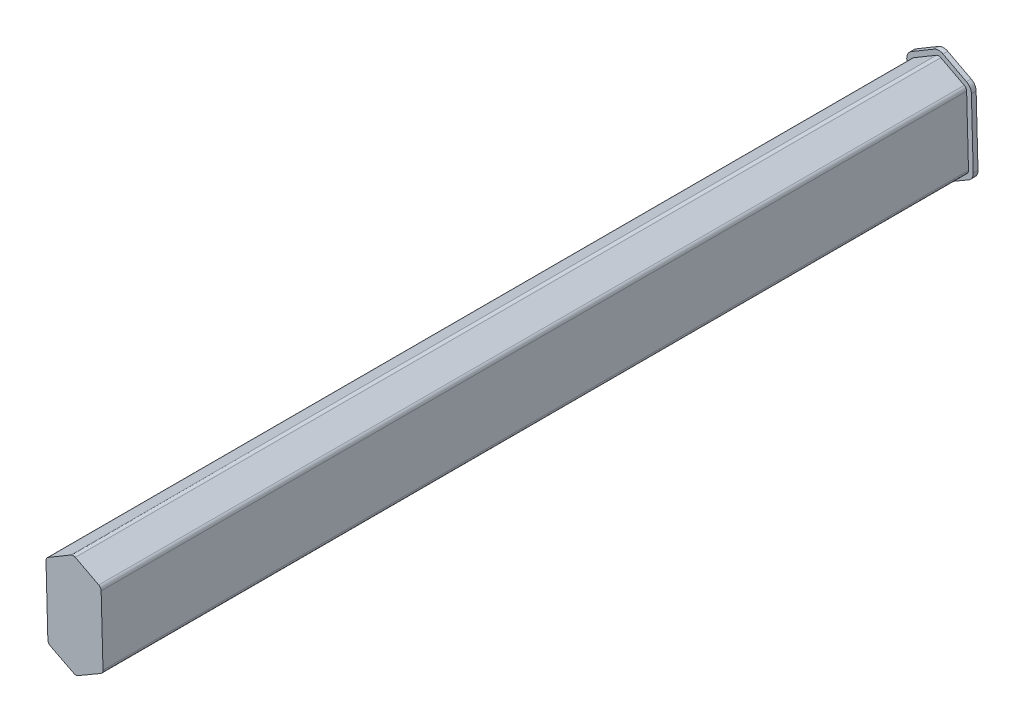
SolidWorks part; units mm, degrees
other "Markup1"
sketch "Sketch4" plane through (238.7089, 157.952, 185) normal (0.151, -0.0403, 0.9877) x (-0.3193, -0.9476, 0.0101)
ref_plane "Front Plane" through (0, 0, 0) normal (0, 0, 1) x (1, 0, 0)
ref_plane "Top Plane" through (0, 0, 0) normal (0, 1, 0) x (1, 0, 0)
ref_plane "Right Plane" through (0, 0, 0) normal (1, 0, 0) x (0, 0, -1)
sketch "Sketch1" plane through (0, 0, 0) normal (0, 0, 1) x (1, 0, 0)
  line L0 (36.798, 101.1427) -> (103.7813, 99.6461) construction
  line L1 (229.8883, 157.752) -> (228.9956, 190.3868) construction
  line L31 (229.4664, 190.0848) -> (234.3884, 187.5166)
  line L32 (228.5166, 190.1025) -> (223.7423, 187.2691) construction
  line L33 (223.253, 186.3818) -> (223.6425, 172.1409) construction
  line L34 (224.1866, 171.2781) -> (229.1073, 168.7597) construction
  line L35 (234.8421, 171.5695) -> (230.0664, 168.7859) construction
  line L36 (234.9486, 186.7017) -> (235.3382, 172.4608) construction
  line L37 (229.4895, 190.1291) -> (234.4116, 187.5609) construction
  line L38 (234.8986, 186.7003) -> (235.2882, 172.4595)
  line L39 (234.8169, 171.6127) -> (230.0413, 168.8291)
  line L40 (224.2093, 171.3226) -> (229.1301, 168.8042)
  line L41 (223.303, 186.3831) -> (223.6925, 172.1423)
  line L42 (228.5421, 190.0595) -> (223.7678, 187.2261)
  arc A0 (223.253, 186.3818) -> (223.7423, 187.2691) centre (224.2526, 186.4091) cw construction
  arc A15 (234.4116, 187.5609) -> (234.9486, 186.7017) centre (233.949, 186.6744) cw construction
  arc A16 (235.3382, 172.4608) -> (234.8421, 171.5695) centre (234.3385, 172.4335) cw construction
  arc A17 (224.1866, 171.2781) -> (223.6425, 172.1409) centre (224.6422, 172.1682) cw construction
  arc A18 (229.1073, 168.7597) -> (230.0664, 168.7859) centre (229.5629, 169.6499) ccw construction
  arc A19 (228.5166, 190.1025) -> (229.4895, 190.1291) centre (229.0269, 189.2425) cw construction
  arc A20 (234.3884, 187.5166) -> (234.8986, 186.7003) centre (233.949, 186.6744) cw
  arc A21 (235.2882, 172.4595) -> (234.8169, 171.6127) centre (234.3385, 172.4335) cw
  arc A22 (229.1301, 168.8042) -> (230.0413, 168.8291) centre (229.5629, 169.6499) ccw
  arc A23 (224.2093, 171.3226) -> (223.6925, 172.1423) centre (224.6422, 172.1682) cw
  arc A24 (223.303, 186.3831) -> (223.7678, 187.2261) centre (224.2526, 186.4091) cw
  arc A25 (228.5421, 190.0595) -> (229.4664, 190.0848) centre (229.0269, 189.2425) cw
  point P24 (223.2369, 186.9692)
  point P27 (234.9326, 187.2891)
  point P30 (235.3544, 171.8681)
  point P33 (223.6588, 171.5482)
  point P36 (229.594, 168.5105)
  point P39 (228.9956, 190.3868)
  dimension "D2" = 0.05
  dimension "D1" = 67
extrude "Boss-Extrude1" add sketch "Sketch1" along normal blind 182 contours L32 A0 L33 A17 L34 A18 L35 A16 L36 A15 L37 A19
sketch "Sketch5" plane through (0, 0, 0) normal (0, 0, -1) x (-1, 0, 0)
  line L25 (-229.929, 190.9713) -> (-234.851, 188.4032)
  line L26 (-235.8983, 186.7277) -> (-236.2878, 172.4868)
  line L27 (-235.3205, 170.7488) -> (-230.5448, 167.9652)
  line L28 (-228.6745, 167.914) -> (-223.7538, 170.4324)
  line L29 (-222.6929, 172.1149) -> (-222.3033, 186.3558)
  line L30 (-223.2574, 188.086) -> (-228.0317, 190.9195)
  line L31 (-229.929, 190.9713) -> (-234.851, 188.4032)
  line L32 (-235.8983, 186.7277) -> (-236.2878, 172.4868)
  line L33 (-235.3205, 170.7488) -> (-230.5448, 167.9652)
  line L34 (-228.6745, 167.914) -> (-223.7538, 170.4324)
  line L35 (-222.6929, 172.1149) -> (-222.3033, 186.3558)
  line L36 (-223.2574, 188.086) -> (-228.0317, 190.9195)
  arc A24 (-228.0317, 190.9195) -> (-229.929, 190.9713) centre (-229.0269, 189.2425) ccw
  arc A25 (-234.851, 188.4032) -> (-235.8983, 186.7277) centre (-233.949, 186.6744) ccw
  arc A26 (-236.2878, 172.4868) -> (-235.3205, 170.7488) centre (-234.3385, 172.4335) ccw
  arc A27 (-230.5448, 167.9652) -> (-228.6745, 167.914) centre (-229.5629, 169.6499) ccw
  arc A28 (-223.7538, 170.4324) -> (-222.6929, 172.1149) centre (-224.6422, 172.1682) ccw
  arc A29 (-222.3033, 186.3558) -> (-223.2574, 188.086) centre (-224.2526, 186.4091) ccw
  arc A30 (-228.0317, 190.9195) -> (-229.929, 190.9713) centre (-229.0269, 189.2425) ccw
  arc A31 (-234.851, 188.4032) -> (-235.8983, 186.7277) centre (-233.949, 186.6744) ccw
  arc A32 (-236.2878, 172.4868) -> (-235.3205, 170.7488) centre (-234.3385, 172.4335) ccw
  arc A33 (-230.5448, 167.9652) -> (-228.6745, 167.914) centre (-229.5629, 169.6499) ccw
  arc A34 (-223.7538, 170.4324) -> (-222.6929, 172.1149) centre (-224.6422, 172.1682) ccw
  arc A35 (-222.3033, 186.3558) -> (-223.2574, 188.086) centre (-224.2526, 186.4091) ccw
  dimension "D1" = 1
extrude "Boss-Extrude2" add sketch "Sketch5" along normal blind 1
ref_plane "Plane3" through (234.0283, 6.4016, 0) normal (0.9996, 0.0273, 0) x (0, 0, -1)
ref_plane "Plane4" through (-5.3848, 172.0812, 0) normal (-0.0313, 0.9995, 0) x (0.9995, 0.0313, 0)
